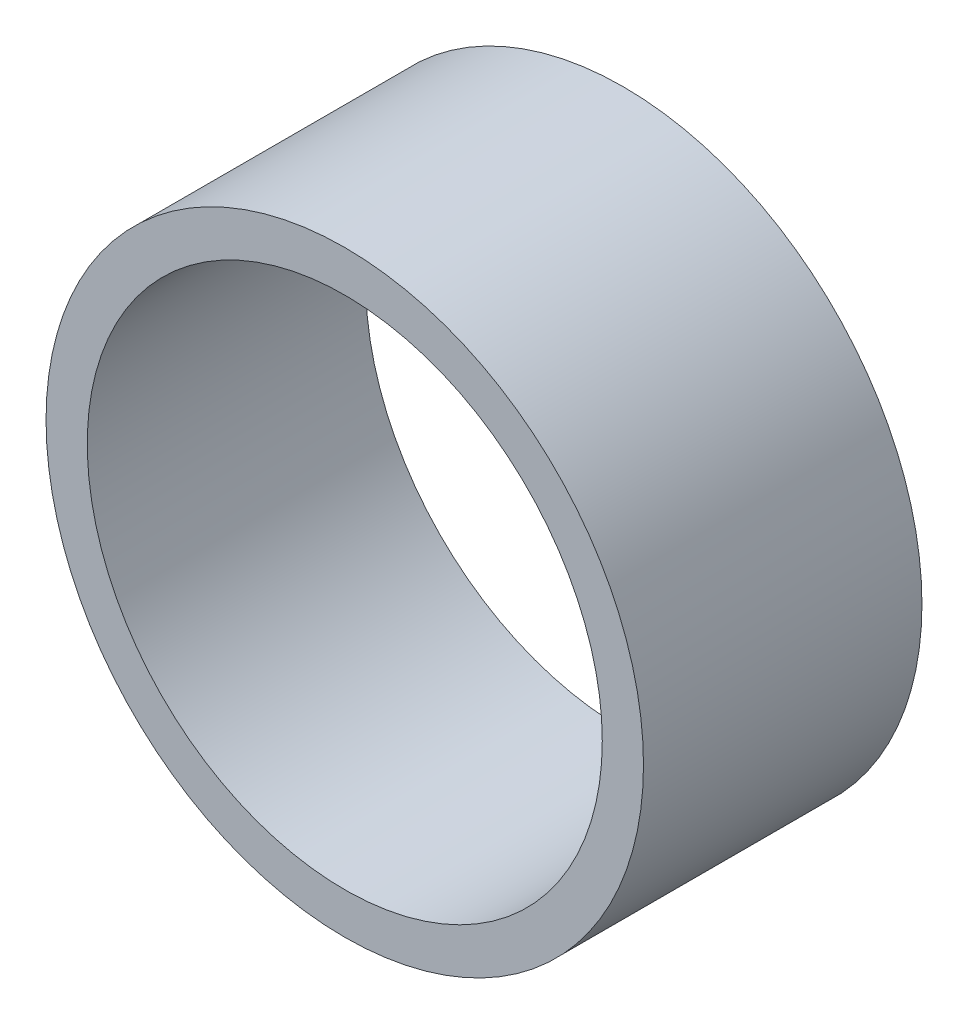
SolidWorks part; units mm, degrees
material "Silicon"
ref_plane "Front" through (0, 0, 0) normal (0, 0, 1) x (1, 0, 0)
ref_plane "Top" through (0, 0, 0) normal (0, 1, 0) x (1, 0, 0)
ref_plane "Right" through (0, 0, 0) normal (1, 0, 0) x (0, 0, -1)
sketch "Sketch1" plane through (0, 0, 0) normal (0, 0, 1) x (1, 0, 0)
  circle A0 centre (0, 0) radius 87
  circle A1 centre (0, 0) radius 75
extrude "Boss-Extrude1" add sketch "Sketch1" along normal blind 81.1
